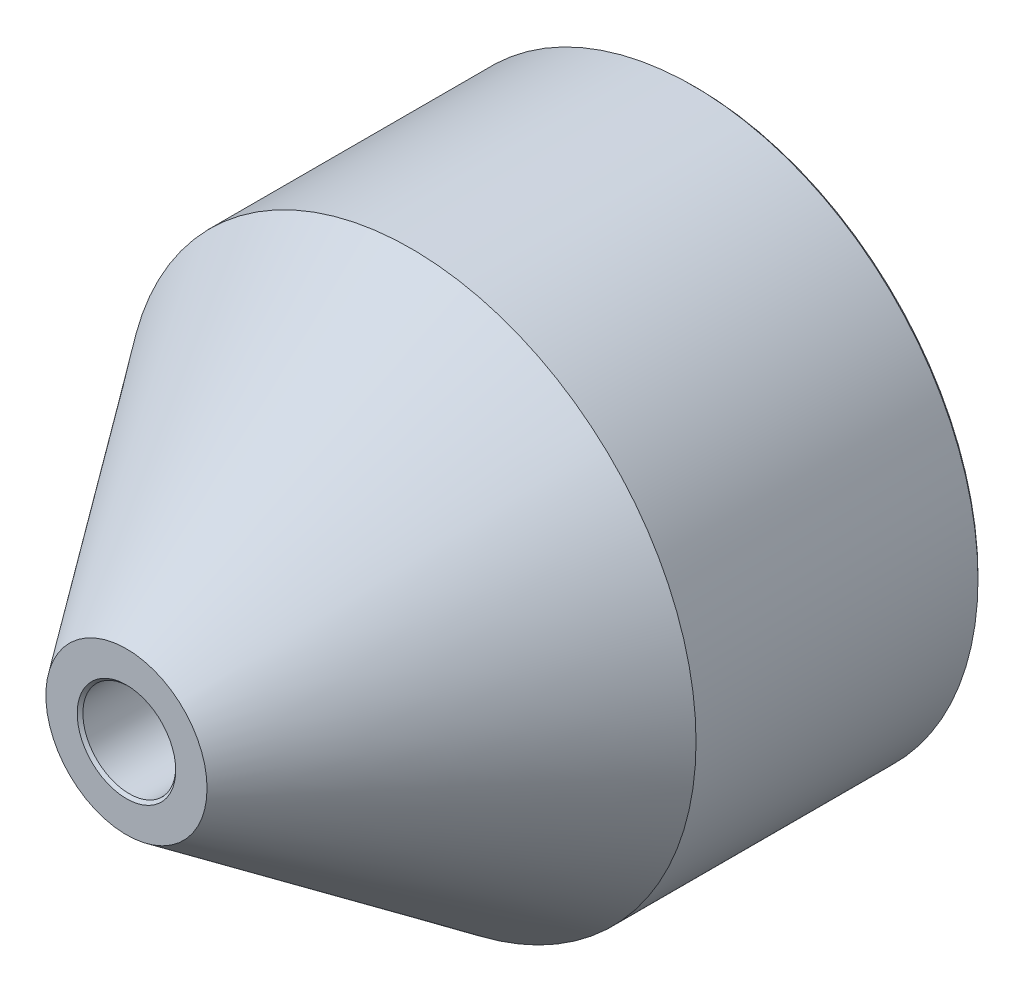
SolidWorks part; units mm, degrees
ref_plane "Front Plane" through (0, 0, 0) normal (0, 0, 1) x (1, 0, 0)
ref_plane "Top Plane" through (0, 0, 0) normal (0, 1, 0) x (1, 0, 0)
ref_plane "Right Plane" through (0, 0, 0) normal (1, 0, 0) x (0, 0, -1)
sketch "Sketch1" plane through (0, 0, 0) normal (0, 1, 0) x (1, 0, 0)
  line L0 (0, 27.7365) -> (4.15, 27.7365)
  line L1 (0, -55) -> (0, 55) construction
  line L2 (4.15, 27.7365) -> (4.15, 37.7365)
  line L3 (4.15, 37.7365) -> (50, 37.7365)
  line L4 (50, 37.7365) -> (50, -12.2635)
  line L5 (50, -12.2635) -> (14.15, -62.2635)
  line L6 (14.15, -62.2635) -> (8.15, -62.2635)
  line L7 (8.15, -62.2635) -> (8.15, -12.2635)
  line L8 (8.15, -12.2635) -> (0, -12.2635)
  line L9 (0, -12.2635) -> (0, 27.7365)
  dimension "D1" = 4.15
  dimension "D2" = 10
  dimension "D3" = 50
  dimension "D4" = 50
  dimension "D5" = 8.15
  dimension "D6" = 50
  dimension "D7" = 50
  dimension "D8" = 6
revolve "Revolve1" add sketch "Sketch1" angle 360 about L9
chamfer "Chamfer1" distance 0.5 angle 45 3 edges at (8.15, 0, 62.2635) (50, 0, -37.7365) (4.15, 0, -37.7365)
